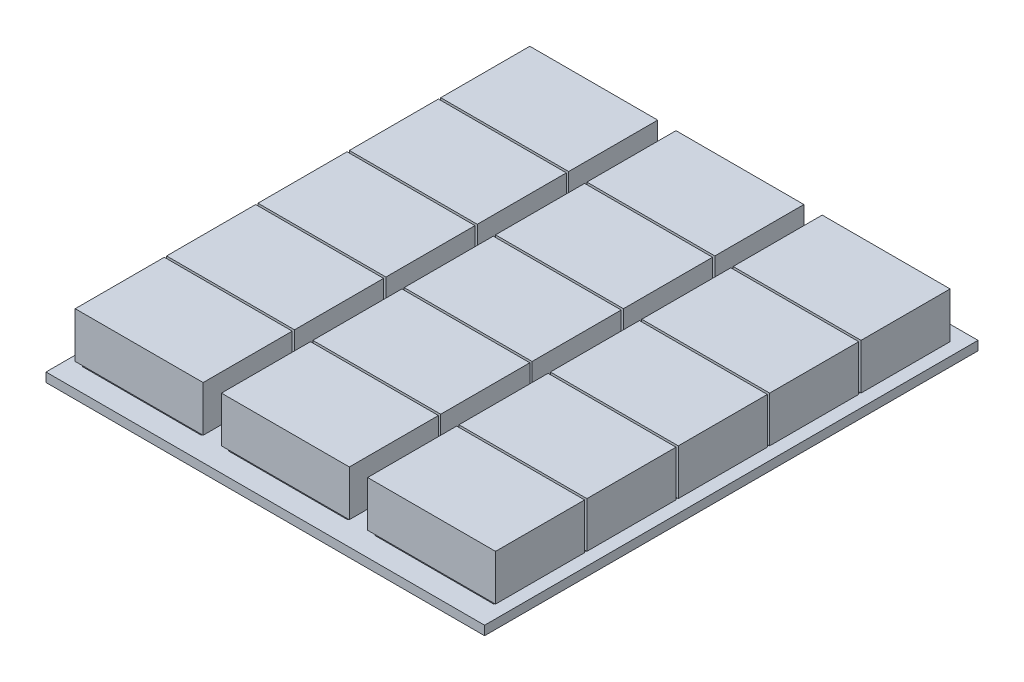
SolidWorks part; units mm, degrees
ref_plane "Front Plane" through (0, 0, 0) normal (0, 0, 1) x (1, 0, 0)
ref_plane "Top Plane" through (0, 0, 0) normal (0, 1, 0) x (1, 0, 0)
ref_plane "Right Plane" through (0, 0, 0) normal (1, 0, 0) x (0, 0, -1)
sketch "Sketch1" plane through (0, 0, 0) normal (0, 1, 0) x (1, 0, 0)
  line L1 (-40, -135) -> (40, -135)
  line L2 (-40, -135) -> (-40, 135)
  line L3 (-40, 135) -> (40, 135)
  line L4 (40, -135) -> (40, 135)
  line L5 (-40, -135) -> (40, 135) construction
  line L6 (-40, 135) -> (40, -135) construction
  point P0 (0, 0)
  dimension "D1" = 80
  dimension "D2" = 270
extrude "Boss-Extrude1" add sketch "Sketch1" along normal blind 5
sketch "Sketch2" plane through (0, 5, 0) normal (0, 1, 0) x (1, 0, 0)
  line L0 (0, 0) -> (0, -135) construction
  line L1 (-40, -135) -> (40, -135) construction
  line L3 (-32.5, -77.5) -> (32.5, -77.5)
  line L4 (-32.5, -77.5) -> (-32.5, -122.5)
  line L5 (-32.5, -122.5) -> (32.5, -122.5)
  line L6 (32.5, -77.5) -> (32.5, -122.5)
  line L7 (-32.5, -77.5) -> (32.5, -122.5) construction
  line L8 (-32.5, -122.5) -> (32.5, -77.5) construction
  point P5 (0, -100)
  dimension "D1" = 65
  dimension "D2" = 45
  dimension "D3" = 12.5
extrude "Boss-Extrude3" add sketch "Sketch2" along normal blind 2
pattern_linear "LPattern1" count 5 spacing 50 along (0, 0, -1) of "Boss-Extrude3"
sketch "Sketch3" plane through (0, 7, 0) normal (0, 1, 0) x (1, 0, 0)
  line L0 (0, 0) -> (0, -122.5) construction
  line L1 (-32.5, -122.5) -> (32.5, -122.5) construction
  line L2 (-40, 135) -> (-40, -135) construction
  line L3 (-35, -75.2605) -> (35, -75.2605)
  line L4 (-35, -75.2605) -> (-35, -124.0095)
  line L5 (-35, -124.0095) -> (35, -124.0095)
  line L6 (35, -75.2605) -> (35, -124.0095)
  line L7 (-35, -75.2605) -> (35, -124.0095) construction
  line L8 (-35, -124.0095) -> (35, -75.2605) construction
  point P5 (0, -99.635)
  dimension "D1" = 5
extrude "Boss-Extrude8" add sketch "Sketch3" along normal blind 25
pattern_linear "LPattern5" count 5 spacing 50 along (0, 0, -1) of "Boss-Extrude8"
pattern_linear "LPattern6" count 3 spacing 80 along (-1, 0, 0) of "Boss-Extrude1", "Boss-Extrude3", "LPattern1", "Boss-Extrude8", "LPattern5"
